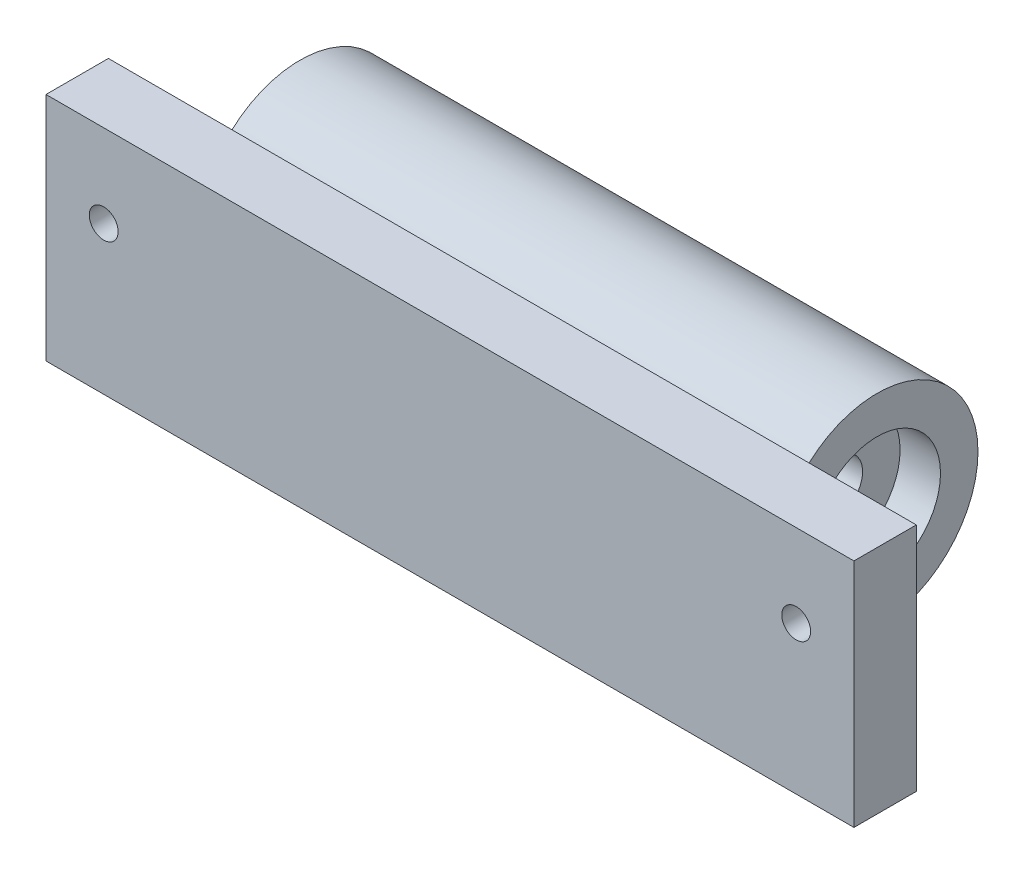
SolidWorks part; units mm, degrees
ref_plane "Спереди" through (0, 0, 0) normal (0, 0, 1) x (1, 0, 0)
ref_plane "Сверху" through (0, 0, 0) normal (0, 1, 0) x (1, 0, 0)
ref_plane "Справа" through (0, 0, 0) normal (1, 0, 0) x (0, 0, -1)
sketch "Эскиз1" plane through (0, 0, 0) normal (1, 0, 0) x (0, 0, -1)
  line L1 (-24, 14.3533) -> (-13.1889, 14.3533)
  line L2 (-24, 14.3533) -> (-24, -25.6467)
  line L3 (-24, -25.6467) -> (-13.1889, -25.6467)
  line L4 (-13.1889, 14.3533) -> (-13.1889, 11.5023)
  line L8 (-13.1889, -11.5023) -> (-13.1889, -25.6467)
  circle A0 centre (0, 0) radius 4.5
  arc A1 (-13.1889, -11.5023) -> (-13.1889, 11.5023) centre (0, 0) ccw
  point P4 (-17.5, 0)
  dimension "D1" = 9
  dimension "D2" = 35
  dimension "D3" = 40
extrude "Бобышка-Вытянуть1" add sketch "Эскиз1" along normal blind 100
sketch "Эскиз2" plane through (0, 0, 0) normal (-1, 0, 0) x (0, 0, 1)
  line L1 (24, 14.3533) -> (13.1889, 14.3533)
  line L2 (24, 14.3533) -> (24, -25.6467)
  line L3 (24, -25.6467) -> (13.1889, -25.6467)
  line L4 (13.1889, 14.3533) -> (13.1889, -25.6467)
extrude "Бобышка-Вытянуть2" add sketch "Эскиз2" along normal blind 20
sketch "Эскиз3" plane through (100, 0, 0) normal (1, 0, 0) x (0, 0, -1)
  line L1 (-24, 14.3533) -> (-13.1889, 14.3533)
  line L2 (-24, 14.3533) -> (-24, -25.6467)
  line L3 (-24, -25.6467) -> (-13.1889, -25.6467)
  line L4 (-13.1889, 14.3533) -> (-13.1889, -25.6467)
extrude "Бобышка-Вытянуть3" add sketch "Эскиз3" along normal blind 20
sketch "Эскиз4" plane through (0, 0, 13.1889) normal (0, 0, -1) x (-1, 0, 0)
  line L0 (-120, 26.7137) -> (-100, 26.7137) construction
  line L1 (-100, 26.7137) -> (0, 26.7137) construction
  line L2 (0, 26.7137) -> (20, 26.7137) construction
  circle A0 centre (-110, 0) radius 2.5
  circle A1 centre (10, 0) radius 2.5
  dimension "D1" = 5
  dimension "D2" = 5
extrude "Вырез-Вытянуть1" cut sketch "Эскиз4" against normal through all
sketch "Эскиз5" plane through (0, 0, 13.1889) normal (0, 0, -1) x (-1, 0, 0)
  circle A0 centre (-110, 0) radius 4.25
  circle A1 centre (10, 0) radius 4.25
  dimension "D1" = 8.5
  dimension "D2" = 8.5
extrude "Вырез-Вытянуть2" cut sketch "Эскиз5" against normal blind 5
sketch "Эскиз6" plane through (100, 0, 0) normal (1, 0, 0) x (0, 0, -1)
  circle A0 centre (0, 0) radius 11
  dimension "D1" = 22
extrude "Вырез-Вытянуть3" cut sketch "Эскиз6" against normal blind 7
sketch "Эскиз7" plane through (0, 0, 0) normal (-1, 0, 0) x (0, 0, 1)
  circle A0 centre (0, 0) radius 11
  dimension "D1" = 22
extrude "Вырез-Вытянуть4" cut sketch "Эскиз7" against normal blind 7
